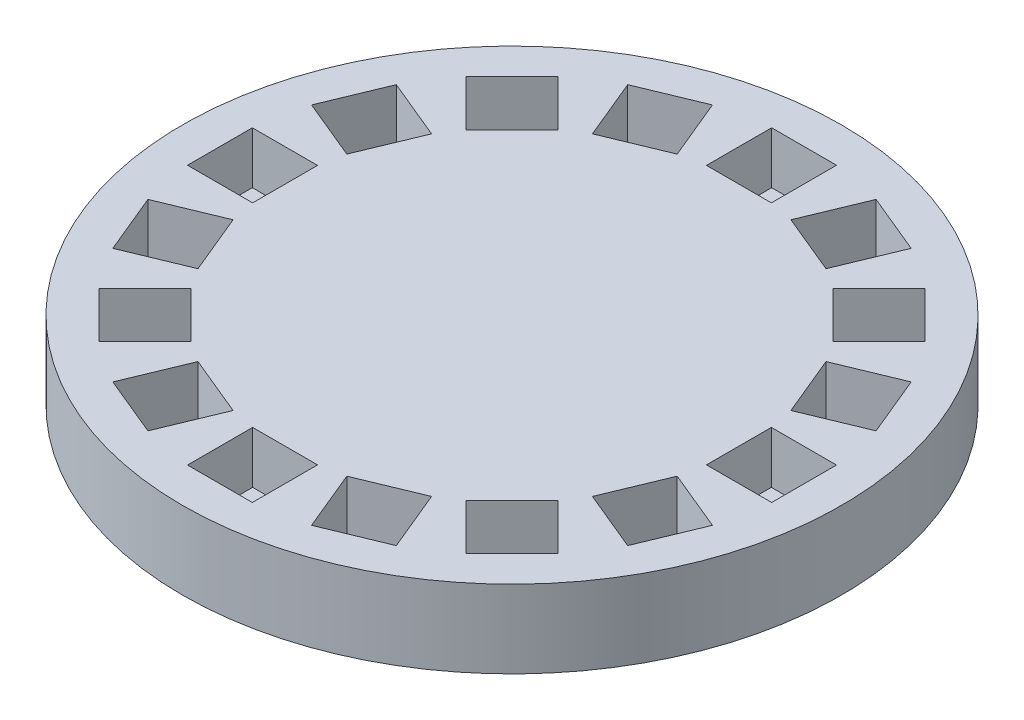
SolidWorks part; units mm, degrees
ref_plane "Front Plane" through (0, 0, 0) normal (0, 0, 1) x (1, 0, 0)
ref_plane "Top Plane" through (0, 0, 0) normal (0, 1, 0) x (1, 0, 0)
ref_plane "Right Plane" through (0, 0, 0) normal (1, 0, 0) x (0, 0, -1)
sketch "Sketch1" plane through (0, 0, 0) normal (0, 1, 0) x (1, 0, 0)
  circle A0 centre (0, 0) radius 63.5
  dimension "D1" = 127
extrude "Boss-Extrude1" add sketch "Sketch1" along normal blind 14.9734
sketch "Sketch2" plane through (0, 14.9734, 0) normal (0, 1, 0) x (1, 0, 0)
  line L0 (0, 0) -> (0, -50) construction
  line L1 (-6.25, -56.28) -> (6.25, -56.28)
  line L2 (-6.25, -56.28) -> (-6.25, -43.72)
  line L3 (-6.25, -43.72) -> (6.25, -43.72)
  line L4 (6.25, -56.28) -> (6.25, -43.72)
  line L5 (-6.25, -56.28) -> (6.25, -43.72) construction
  line L6 (-6.25, -43.72) -> (6.25, -56.28) construction
  point P0 (0, -50)
  dimension "D1" = 12.5
  dimension "D2" = 12.56
  dimension "D3" = 50
extrude "Cut-Extrude1" cut sketch "Sketch2" against normal blind 10
pattern_circular "CirPattern1" count 16 over 360 about axis through (0, 0, 0) along (0, 1, 0) of "Cut-Extrude1"
sketch "Sketch5" plane through (0, 0, 0) normal (0, 1, 0) x (1, 0, 0)
  line L0 (-56.28, 0) -> (-63.5, 0) construction
  line L1 (-56.28, 6.25) -> (-56.28, -6.25) construction
  circle A0 centre (0, 0) radius 63.5 construction
equation "\"line\"= 5"
equation "\"D3@Sketch2\"=\"line\""
